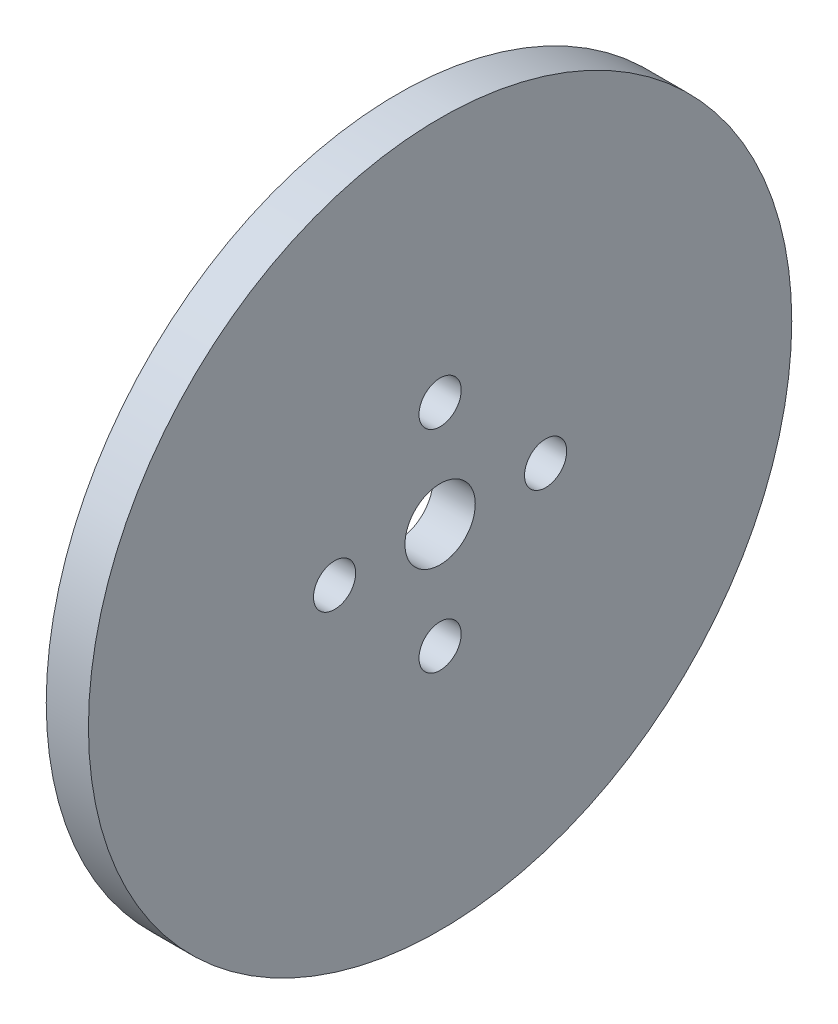
SolidWorks part; units mm, degrees
ref_plane "Alzado" through (0, 0, 0) normal (0, 0, 1) x (1, 0, 0)
ref_plane "Planta" through (0, 0, 0) normal (0, 1, 0) x (1, 0, 0)
ref_plane "Vista lateral" through (0, 0, 0) normal (1, 0, 0) x (0, 0, -1)
sketch "Croquis1" plane through (0, 0, 0) normal (1, 0, 0) x (0, 0, -1)
  line L0 (0, 0) -> (0, 7.5) construction
  circle A0 centre (0, 0) radius 25
  circle A1 centre (0, 0) radius 2.5
  circle A2 centre (0, 7.5) radius 1.5
  circle A3 centre (7.5, 0) radius 1.5
  circle A4 centre (0, -7.5) radius 1.5
  circle A5 centre (-7.5, 0) radius 1.5
  point P15 (0, 0)
  dimension "D1" = 4
extrude "Saliente-Extruir1" add sketch "Croquis1" along normal blind 3
